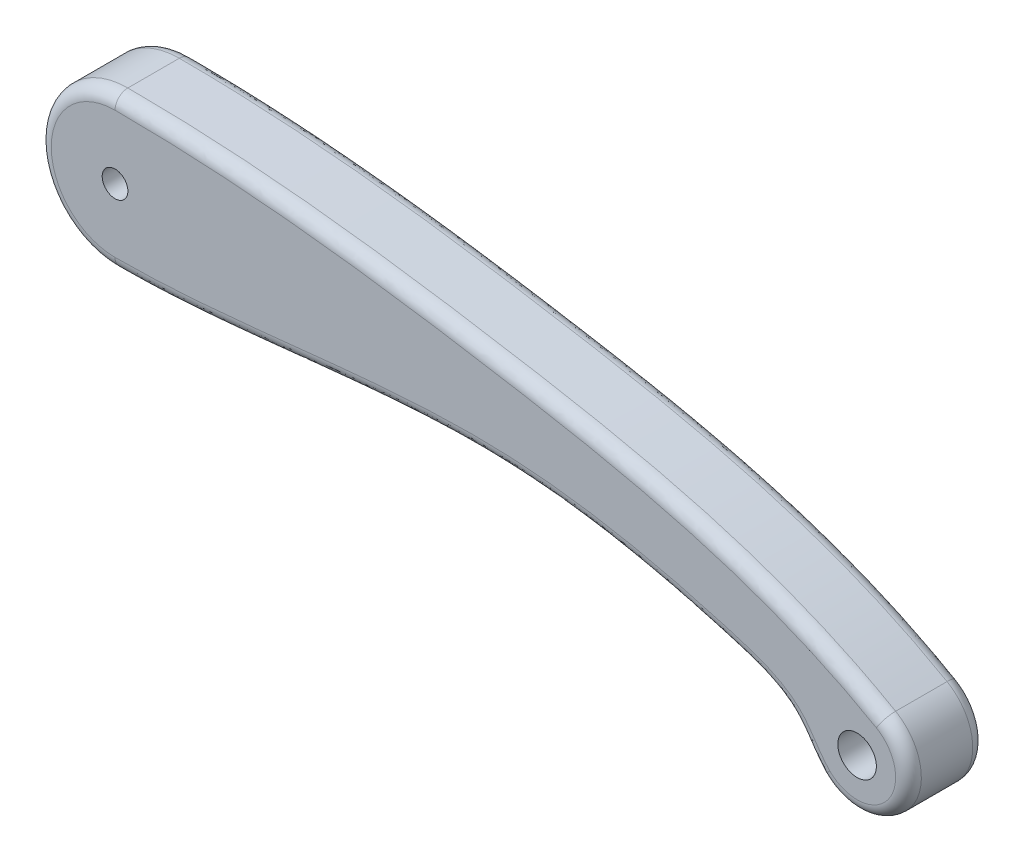
SolidWorks part; units mm, degrees
ref_plane "Alzado" through (0, 0, 0) normal (0, 0, 1) x (1, 0, 0)
ref_plane "Planta" through (0, 0, 0) normal (0, 1, 0) x (1, 0, 0)
ref_plane "Vista lateral" through (0, 0, 0) normal (1, 0, 0) x (0, 0, -1)
sketch "Croquis1" plane through (0, 0, 0) normal (0, 0, 1) x (1, 0, 0)
  line L0 (28.869, -4.8178) -> (29.869, -3.0857) construction
  line L1 (28.869, -4.8178) -> (24.3374, -2.7047) construction
  line L2 (28.869, -4.8178) -> (26.369, -4.8178) construction
  line L4 (0, 0) -> (15, -0.5044) construction
  line L5 (15, -0.5044) -> (15, 1.4956)
  line L6 (15, -0.5044) -> (15, -2.0044)
  line L8 (24.3374, -2.7047) -> (23.8714, -3.5894)
  line L9 (28.869, -4.8178) -> (27.4548, -6.232) construction
  arc A0 (0, 2.98) -> (0, -2.98) centre (0, 0) ccw
  circle A2 centre (0, 0) radius 0.5
  arc A3 (27.4548, -6.232) -> (29.869, -3.0857) centre (28.869, -4.8178) ccw
  circle A4 centre (28.869, -4.8178) radius 0.75
  spline S0 degree 3 poles (27.4548, -6.232) (26.9988, -5.776) (26.3765, -4.3742) (21.7203, -2.8679) (13.1414, -1.1413) (4.9795, -2.98) (0, -2.98) knots 0 0 0 0 0.06232 0.159606 0.474597 1 1 1 1
  spline S1 degree 3 poles (29.869, -3.0857) (25.2235, -0.4037) (15.1128, 1.6494) (5.1861, 2.98) (0, 2.98) knots 0 0 0 0 0.507924 1 1 1 1
  dimension "D1" = 5.96
  dimension "D2" = 15
  dimension "D5" = 1.5
  dimension "D8" = 1
  dimension "D3" = 1.5
  dimension "D4" = 2
  dimension "D6" = 2.5
  dimension "D7" = 60
  dimension "D9" = 25
  dimension "D10" = 5
  dimension "D11" = 1
extrude "Saliente-Extruir1" add sketch "Croquis1" along normal blind 3
fillet "Redondeo1" radius 0.5 4 edges at (30.4557, -6.0353, 3) (-2.98, 0, 3)
fillet "Redondeo2" radius 0.5 4 edges at (-2.98, 0, 0) (30.4557, -6.0353, 0)
